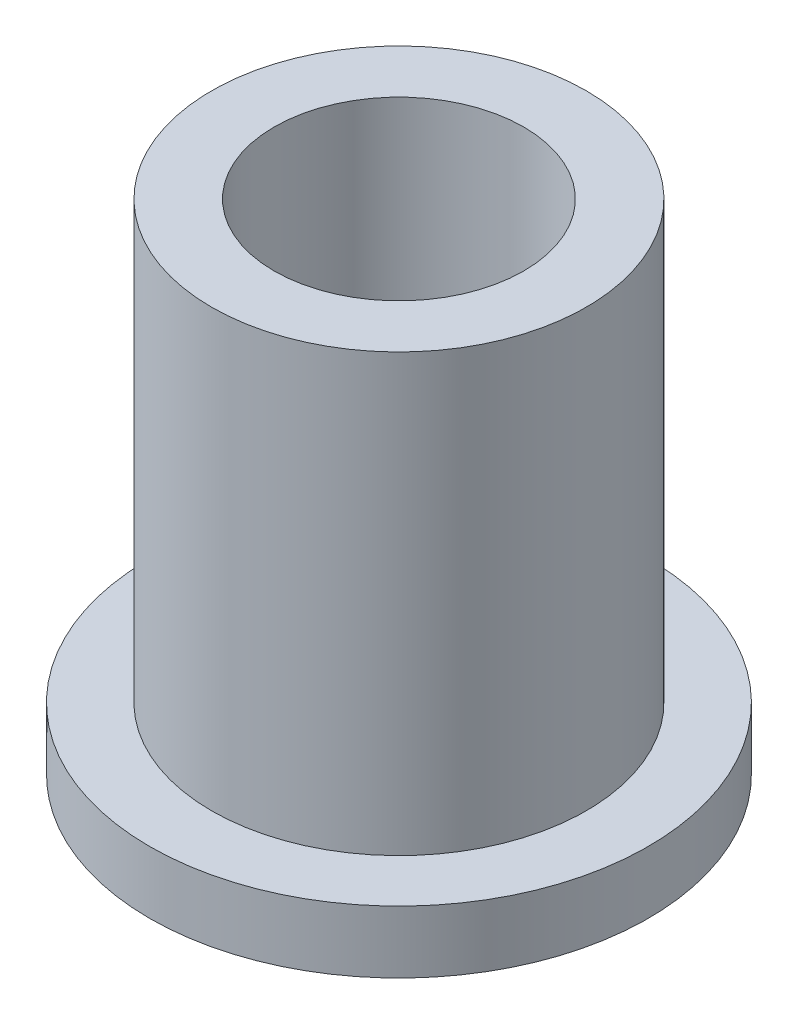
SolidWorks part; units mm, degrees
ref_plane "Front" through (0, 0, 0) normal (0, 0, 1) x (1, 0, 0)
ref_plane "Top" through (0, 0, 0) normal (0, 1, 0) x (1, 0, 0)
ref_plane "Right" through (0, 0, 0) normal (1, 0, 0) x (0, 0, -1)
sketch "Sketch1" plane through (0, 0, 0) normal (0, 1, 0) x (1, 0, 0)
  circle A0 centre (0, 0) radius 4.005
  circle A1 centre (0, 0) radius 6.015
  circle A2 centre (0, 0) radius 8
  dimension "ID" = 8.01
  dimension "OD" = 12.03
  dimension "FlangeOD" = 16
sketch "Sketch2" plane through (0, 0, 0) normal (0, 1, 0) x (1, 0, 0)
  circle A0 centre (0, 0) radius 4.005 construction
  circle A1 centre (0, 0) radius 6.015 construction
  circle A2 centre (0, 0) radius 4.005
  circle A3 centre (0, 0) radius 6.015
extrude "Boss-Extrude1" add sketch "Sketch2" along normal blind 16
sketch "Sketch3" plane through (0, 0, 0) normal (0, 1, 0) x (1, 0, 0)
  circle A0 centre (0, 0) radius 8 construction
  circle A1 centre (0, 0) radius 6.015 construction
  circle A2 centre (0, 0) radius 8
  circle A3 centre (0, 0) radius 6.015
extrude "Boss-Extrude2" add sketch "Sketch3" along normal blind 2
